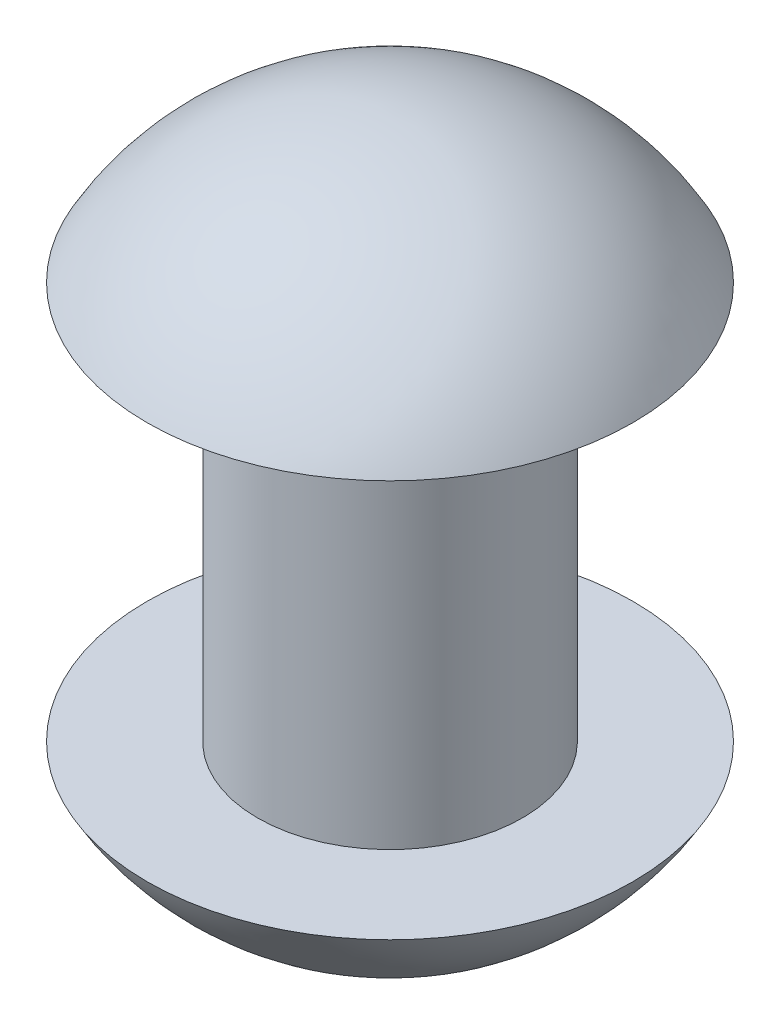
SolidWorks part; units mm, degrees
ref_plane "Ebene vorne" through (0, 0, 0) normal (0, 0, 1) x (1, 0, 0)
ref_plane "Ebene oben" through (0, 0, 0) normal (0, 1, 0) x (1, 0, 0)
ref_plane "Ebene rechts" through (0, 0, 0) normal (1, 0, 0) x (0, 0, -1)
sketch "Sketch1" plane through (0, 0, 0) normal (0, 0, 1) x (1, 0, 0)
  line L0 (-0.12, 0) -> (-0.12, 0.36)
  line L1 (-0.12, 0.36) -> (-0.22, 0.36)
  line L3 (0, 0.3701) -> (0, 0.18) construction
  line L4 (-0.12, 0) -> (-0.22, 0)
  line L8 (0, 0.4889) -> (0, -0.1289)
  line L9 (0, 0.18) -> (-0.3429, 0.18) construction
  arc A0 (-0.22, 0.36) -> (0, 0.4889) centre (0, 0.2368) cw
  arc A2 (-0.22, 0) -> (0, -0.1289) centre (0, 0.1232) ccw
  point P10 (-0.12, 0.18)
  dimension "D1" = 0.12
  dimension "D2" = 0.1
  dimension "D3" = 0.36
revolve "Revolve1" add sketch "Sketch1" angle 360 about L8
